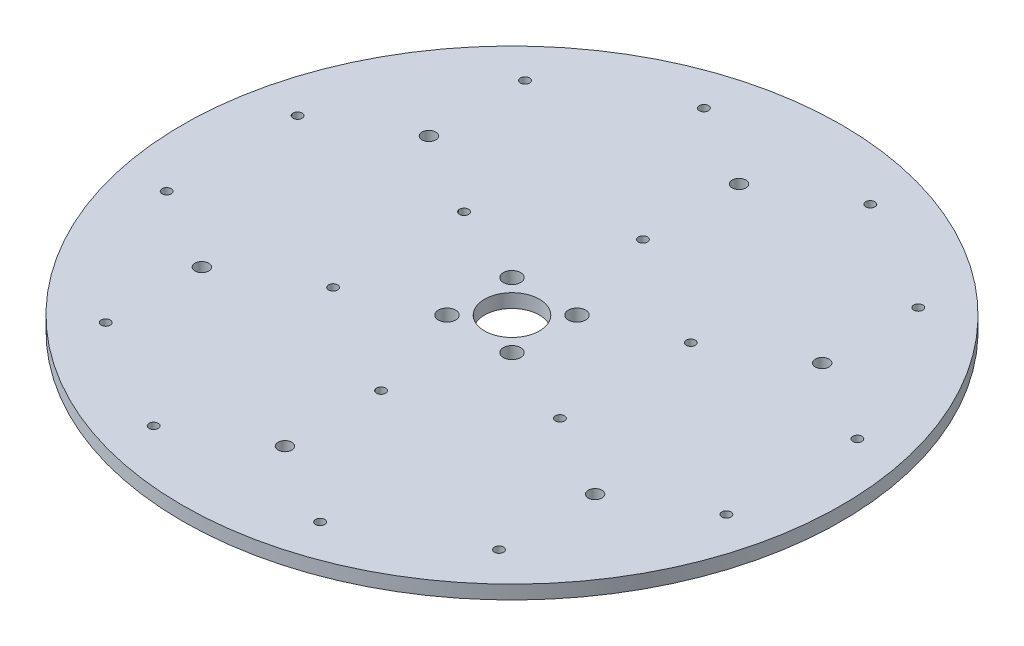
SolidWorks part; units mm, degrees
material "6061-T6 (SS)"
ref_plane "Front Plane" through (0, 0, 0) normal (0, 0, 1) x (1, 0, 0)
ref_plane "Top Plane" through (0, 0, 0) normal (0, 1, 0) x (1, 0, 0)
ref_plane "Right Plane" through (0, 0, 0) normal (1, 0, 0) x (0, 0, -1)
sketch "Sketch1" plane through (0, 0, 0) normal (0, 1, 0) x (1, 0, 0)
  circle A0 centre (0, 0) radius 152.4
  dimension "D1" = 304.8
extrude "Boss-Extrude1" add sketch "Sketch1" along normal blind 6.35
sketch "Sketch2" plane through (0, 6.35, 0) normal (0, 1, 0) x (1, 0, 0)
  line L0 (0, 0) -> (245.5083, 0) construction
  line L1 (0, 0) -> (0, 105) construction
  line L2 (0, 105) -> (38.4948, 127.225) construction
  circle A0 centre (0, 105) radius 44.45 construction
  circle A1 centre (0, 105) radius 79.375 construction
  circle A2 centre (90.9327, 52.5) radius 79.375 construction
  circle A3 centre (90.9327, -52.5) radius 79.375 construction
  circle A4 centre (0, -105) radius 79.375 construction
  circle A5 centre (-90.9327, -52.5) radius 79.375 construction
  circle A6 centre (-90.9327, 52.5) radius 79.375 construction
  point P3 (-38.4948, 127.225)
  point P6 (38.4948, 127.225)
  point P7 (0, 60.55)
  point P29 (0, 0)
  dimension "D1" = 88.9
  dimension "D4" = 158.75
  dimension "D2" = 105
  dimension "D3" = 120
  dimension "D5" = 6
hole_wizard "M5x0.8 Set Screws" positions "Sketch3" profile "Sketch4" tap size "M5x0.8" standard "ANSI Metric" end condition through all
sketch "Sketch3" plane through (0, 6.35, 0) normal (0, 1, 0) x (1, 0, 0)
  point P0 (-38.4948, 127.225)
  point P3 (38.4948, 127.225)
  point P6 (0, 60.55)
sketch "Sketch4" plane through (-38.4948, 6.35, -127.225) normal (1, 0, 0) x (0, 0, 1)
  line L0 (0, 0) -> (0, 6.35)
  line L1 (0, 6.35) -> (2.1, 6.35)
  line L2 (2.1, 6.35) -> (2.1, 0)
  line L5 (2.1, 0) -> (0, 0)
  line L11 (0, -6.35) -> (0, 107.95) construction
  dimension "Thru Tap Drill Dia." = 4.2
  dimension "Thru Tap Drill Depth" = 6.35
cosmetic thread "Hole Thread1" parameters "D2"=5
cosmetic thread "Hole Thread2" parameters "D2"=5
cosmetic thread "Hole Thread3" parameters "D2"=5
sketch "Sketch5" plane through (0, 6.35, 0) normal (0, 1, 0) x (1, 0, 0)
  circle A0 centre (0, 105) radius 3.175
  dimension "D1" = 6.35
extrude "Cut-Extrude1" cut sketch "Sketch5" against normal through all
pattern_circular "CirPattern1" count 6 over 360 about axis through (0, 0, 0) along (0, 1, 0) of "M5x0.8 Set Screws", "Cut-Extrude1"
sketch "Sketch6" plane through (0, 6.35, 0) normal (0, 1, 0) x (1, 0, 0)
  circle A0 centre (0, 0) radius 12.7
  dimension "D1" = 25.4
extrude "Cut-Extrude2" cut sketch "Sketch6" against normal through all
sketch "Sketch7" plane through (0, 6.35, 0) normal (0, 1, 0) x (1, 0, 0)
  line L0 (0, 0) -> (21.25, 0) construction
  line L1 (0, 0) -> (0, 21.25) construction
  line L2 (0, 0) -> (15.026, 15.026) construction
  circle A0 centre (0, 0) radius 21.25 construction
  point P3 (-15.026, -15.026)
  point P4 (15.026, -15.026)
  point P5 (-15.026, 15.026)
  point P6 (15.026, 15.026)
  dimension "D1" = 42.5
  dimension "D2" = 45
hole_wizard "CBORE for M4 SHCS1" positions "Sketch8" profile "Sketch9" counterbore size "M4" standard "ANSI Metric" end condition through all
sketch "Sketch8" plane through (0, 6.35, 0) normal (0, 1, 0) x (1, 0, 0)
  point P0 (-15.026, 15.026)
  point P3 (15.026, 15.026)
  point P6 (15.026, -15.026)
  point P9 (-15.026, -15.026)
sketch "Sketch9" plane through (-15.026, 6.35, -15.026) normal (1, 0, 0) x (0, 0, 1)
  line L0 (0, 0) -> (0, 6.35)
  line L1 (0, 6.35) -> (2.25, 6.35)
  line L3 (2.25, 6.35) -> (2.25, 6)
  line L4 (2.25, 6) -> (4, 6)
  line L5 (4, 6) -> (4, 0)
  line L7 (4, 0) -> (0, 0)
  line L11 (0, -6.35) -> (0, 107.95) construction
  dimension "Thru Hole Dia." = 4.5
  dimension "Thru Hole Depth" = 6.35
  dimension "C'Bore Dia." = 8
  dimension "C'Bore Depth" = 6
